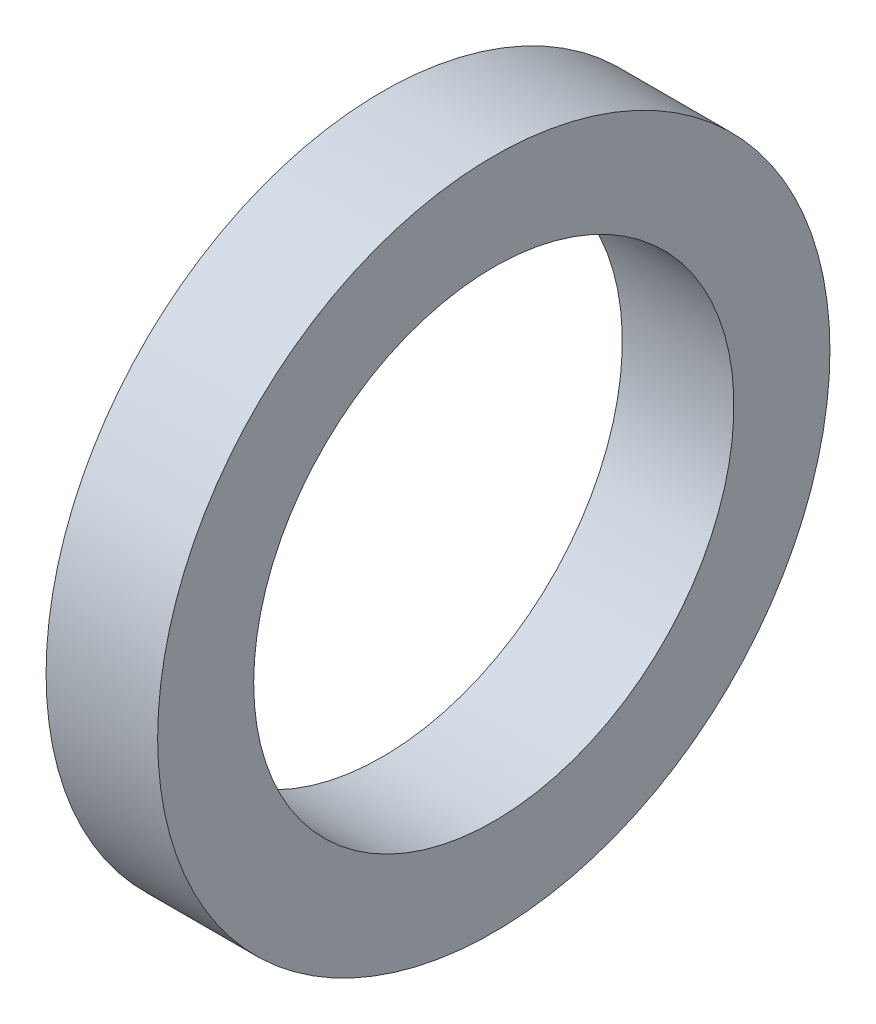
SolidWorks part; units mm, degrees
ref_plane "Front Plane" through (0, 0, 0) normal (0, 0, 1) x (1, 0, 0)
ref_plane "Top Plane" through (0, 0, 0) normal (0, 1, 0) x (1, 0, 0)
ref_plane "Right Plane" through (0, 0, 0) normal (1, 0, 0) x (0, 0, -1)
sketch "Sketch2" plane through (0, 0, 0) normal (0, 0, 1) x (1, 0, 0)
  line L0 (0, 0) -> (58.591, 0) construction
  line L2 (0, 0) -> (18.4, 0)
  line L3 (0, 0) -> (0, 2.5)
  line L4 (0, 2.5) -> (18.4, 2.5)
  line L5 (18.4, 0) -> (18.4, 2.5)
  line L6 (6.0094, 2.5) -> (6.0094, 6)
  line L11 (6.0094, 6) -> (9.9794, 6)
  line L16 (12.9794, 6) -> (12.9794, 3)
  line L17 (12.9794, 3) -> (13.6398, 3)
  line L18 (13.6398, 3) -> (13.6398, 2.5)
  line L19 (13.6398, 2.5) -> (6.0094, 2.5)
  line L22 (13.6398, 2.5) -> (16.1198, 2.5)
  line L23 (13.6398, 2.5) -> (13.6398, 4)
  line L24 (13.6398, 4) -> (16.1198, 4)
  line L25 (16.1198, 2.5) -> (16.1198, 4)
  line L27 (6.0094, 6) -> (9.9794, 6)
  line L28 (6.0094, 6) -> (6.0094, 9)
  line L29 (6.0094, 9) -> (9.9794, 9)
  line L30 (9.9794, 6) -> (9.9794, 9)
  line L31 (6.0094, 9) -> (6.0094, 8.25)
  line L32 (6.0094, 8.25) -> (5.0094, 8.25)
  line L33 (8.6609, 22.001) -> (8.6609, 12.476) construction
  line L34 (5.0094, 12.476) -> (12.3124, 12.476)
  line L35 (9.9794, 9) -> (12.3124, 9)
  line L36 (5.0094, 7.9375) -> (1.7709, 7.9375)
  line L37 (5.0094, 8.25) -> (5.0094, 12.476)
  line L38 (5.0094, 7.9375) -> (5.0094, 13.9365)
  line L39 (5.0094, 13.9365) -> (1.7709, 13.9365)
  line L40 (1.7709, 7.9375) -> (1.7709, 13.9365)
  line L41 (5.0094, 22.001) -> (12.3124, 22.001)
  line L42 (5.0094, 22.001) -> (5.0094, 30.1625)
  line L43 (5.0094, 30.1625) -> (12.3124, 30.1625)
  line L44 (12.3124, 22.001) -> (12.3124, 30.1625)
  line L49 (16.6398, 22.001) -> (16.6398, 7.5)
  line L51 (23.0198, 7.5) -> (23.0198, 6.5)
  line L54 (16.1198, 4) -> (13.6398, 4)
  line L56 (18.0398, 7.5) -> (23.0198, 7.5)
  line L57 (13.3124, 22.001) -> (16.6398, 22.001)
  line L58 (16.1198, 3.5) -> (20.0198, 3.5)
  line L59 (29.9098, 14) -> (26.9098, 11)
  line L60 (4.0094, 31.75) -> (18.0398, 31.75)
  line L61 (18.0398, 7.5) -> (23.0198, 7.5)
  line L62 (18.0398, 7.5) -> (18.0398, 12)
  line L63 (18.0398, 12) -> (23.0198, 12)
  line L64 (23.0198, 7.5) -> (23.0198, 12)
  line L65 (18.0398, 31.75) -> (18.0398, 12)
  line L66 (23.0198, 11) -> (26.9098, 11)
  line L67 (34.8098, 23) -> (31.3098, 19.5)
  line L68 (35.8098, 31) -> (38.7998, 33.99)
  line L69 (29.9098, 14) -> (29.9098, 15)
  line L70 (29.9098, 15) -> (22.9398, 15)
  line L71 (22.9398, 15) -> (21.0398, 15)
  line L72 (18.0398, 7.5) -> (16.6398, 7.5)
  line L73 (21.0398, 15) -> (21.0398, 43)
  line L74 (19.6115, 40) -> (9.6516, 40)
  line L75 (9.6516, 40) -> (4.0094, 40)
  line L76 (21.0398, 43) -> (19.6115, 43)
  line L77 (22.9398, 15) -> (29.9098, 15)
  line L78 (22.9398, 15) -> (22.9398, 21)
  line L79 (22.9398, 21) -> (29.9098, 21)
  line L80 (29.9098, 15) -> (29.9098, 21)
  line L81 (9.6516, 40) -> (19.6115, 40)
  line L82 (9.6516, 40) -> (9.6516, 50)
  line L83 (9.6516, 50) -> (19.6115, 50)
  line L84 (19.6115, 40) -> (19.6115, 50)
  line L85 (4.0094, 40) -> (4.0094, 31.75)
  line L86 (12.9794, 3) -> (12.9794, 2.5)
  line L87 (31.3098, 19.5) -> (29.9098, 19.5)
  line L88 (21.4694, 63.5) -> (21.4694, 51.308)
  line L89 (21.4694, 63.5) -> (25.9398, 63.5)
  line L90 (25.9398, 63.5) -> (25.9398, 25)
  line L91 (27.8398, 25) -> (25.9398, 25)
  line L92 (9.6516, 48) -> (8.2233, 48)
  line L93 (8.2233, 48) -> (8.2233, 53.476)
  line L94 (8.2233, 53.476) -> (19.6115, 53.476)
  line L95 (19.6115, 53.476) -> (19.6115, 50)
  line L96 (13.9174, 63.001) -> (13.9174, 53.476) construction
  line L97 (8.2233, 63.001) -> (19.6115, 63.001)
  line L98 (8.2233, 63.001) -> (8.2233, 68.2625)
  line L99 (8.2233, 68.2625) -> (19.6115, 68.2625)
  line L100 (19.6115, 63.001) -> (19.6115, 68.2625)
  line L101 (12.9794, 6) -> (11.9794, 6)
  line L102 (8.2233, 44.825) -> (4.9848, 44.825)
  line L103 (8.2233, 44.825) -> (8.2233, 54.9365)
  line L104 (8.2233, 54.9365) -> (4.9848, 54.9365)
  line L106 (9.9794, 6) -> (10.8794, 6)
  line L107 (27.8398, 25) -> (34.8098, 25)
  line L108 (34.8098, 25) -> (34.8098, 23)
  line L109 (0, 0) -> (-2, 0)
  line L110 (0, 0) -> (0, 11)
  line L111 (27.8398, 25) -> (34.8098, 25)
  line L112 (27.8398, 25) -> (27.8398, 32.5)
  line L113 (27.8398, 32.5) -> (34.8098, 32.5)
  line L114 (34.8098, 25) -> (34.8098, 32.5)
  line L115 (35.8098, 31) -> (34.8098, 31)
  line L116 (27.8398, 32.5) -> (27.8398, 64.5)
  line L117 (20.5849, 74.025) -> (6.2499, 74.025)
  line L118 (6.2499, 74.025) -> (6.2499, 76.2)
  line L119 (38.7998, 47.29) -> (30.8398, 55.25)
  line L120 (0, 11) -> (-2, 11)
  line L121 (38.7998, 43.815) -> (30.8623, 43.815)
  line L123 (-4.8152, 69.85) -> (1.5348, 76.2)
  line L124 (38.7998, 47.29) -> (38.7998, 33.99)
  line L125 (-2, 0) -> (-2, 11)
  line L126 (38.7998, 37.465) -> (30.8623, 37.465)
  line L127 (30.8623, 43.815) -> (30.8623, 37.465)
  line L128 (6.0094, 2.5) -> (6.0094, 0)
  line L129 (-0.0152, 63.5) -> (-0.0152, 30)
  line L132 (4.9848, 63.5) -> (-0.0152, 63.5)
  line L136 (-1.8152, 30) -> (-11.7752, 30)
  line L138 (-13.7752, 25.4) -> (-2, 25.4)
  line L139 (-2, 25.4) -> (-2, 11.5)
  line L140 (27.8398, 64.5) -> (20.5849, 64.5)
  line L141 (-1.8152, 30) -> (-11.7752, 30)
  line L142 (-1.8152, 30) -> (-1.8152, 39)
  line L143 (-1.8152, 39) -> (-11.7752, 39)
  line L144 (-11.7752, 30) -> (-11.7752, 39)
  line L145 (20.5849, 64.5) -> (20.5849, 74.025)
  line L146 (-12.7752, 37) -> (-12.7752, 47.29)
  line L147 (-12.7752, 37) -> (-11.7752, 37)
  line L148 (30.8398, 55.25) -> (30.8398, 76.2)
  line L149 (11.9794, 6) -> (11.9794, 5.45)
  line L154 (-2, 11.5) -> (0.5, 11.5)
  line L155 (4.9848, 60.6197) -> (24.0348, 60.6197)
  line L160 (4.9848, 60.6197) -> (4.9848, 55.8572)
  line L161 (4.9848, 55.8572) -> (24.0348, 55.8572)
  line L166 (24.0348, 60.6197) -> (24.0348, 55.8572)
  line L167 (4.9848, 60.6197) -> (24.0348, 55.8572) construction
  line L172 (4.9848, 55.8572) -> (24.0348, 60.6197) construction
  line L173 (24.0348, 62.2072) -> (25.9398, 62.2072)
  line L174 (11.9794, 5.45) -> (10.8794, 5.45)
  line L175 (10.8794, 6) -> (10.8794, 5.45)
  line L176 (24.0348, 62.2072) -> (24.0348, 54.2697)
  line L177 (24.0348, 54.2697) -> (25.9398, 54.2697)
  line L178 (25.9398, 62.2072) -> (25.9398, 54.2697)
  line L179 (24.0348, 62.2072) -> (25.9398, 54.2697) construction
  line L180 (24.0348, 54.2697) -> (25.9398, 62.2072) construction
  line L181 (3, 19.6197) -> (15.7, 19.6197)
  line L182 (3, 19.6197) -> (3, 14.8572)
  line L183 (3, 14.8572) -> (15.7, 14.8572)
  line L184 (15.7, 19.6197) -> (15.7, 14.8572)
  line L185 (3, 19.6197) -> (15.7, 14.8572) construction
  line L186 (3, 14.8572) -> (15.7, 19.6197) construction
  line L187 (15.7, 21.2072) -> (16.6398, 21.2072)
  line L188 (15.7, 21.2072) -> (15.7, 13.2697)
  line L189 (15.7, 13.2697) -> (16.6398, 13.2697)
  line L190 (16.6398, 21.2072) -> (16.6398, 13.2697)
  line L191 (15.7, 21.2072) -> (16.6398, 13.2697) construction
  line L192 (15.7, 13.2697) -> (16.6398, 21.2072) construction
  line L193 (0.5, 11.5) -> (0.5, 6.9375)
  line L194 (0.5, 6.9375) -> (1.7709, 6.9375)
  line L195 (23.0198, 6.5) -> (20.0198, 3.5)
  line L196 (4.9848, 63.5) -> (4.9848, 54.9365)
  line L197 (3, 43.825) -> (4.9848, 43.825)
  line L198 (1.7709, 6.9375) -> (1.7709, 7.9375)
  line L199 (6.0094, 0) -> (12.9794, 0)
  line L200 (12.9794, 0) -> (12.9794, 2.5)
  line L201 (18.0398, 31.75) -> (18.0398, 35.875)
  line L202 (18.0398, 35.875) -> (21.0398, 35.875)
  line L203 (30.8398, 76.2) -> (6.2499, 76.2)
  line L204 (2.8049, 69.85) -> (7.2499, 69.85) construction
  line L205 (7.2499, 67.4688) -> (26.2999, 67.4688)
  line L206 (7.2499, 74.025) -> (7.2499, 64.5)
  line L207 (7.2499, 64.5) -> (-1.8152, 64.5)
  line L208 (-1.8152, 64.5) -> (-1.8152, 39)
  line L209 (-12.7752, 47.29) -> (-4.8152, 55.25)
  line L210 (-4.8152, 55.25) -> (-4.8152, 69.85)
  line L211 (7.2499, 67.4688) -> (7.2499, 72.2312)
  line L212 (7.2499, 72.2312) -> (26.2999, 72.2313)
  line L213 (26.2999, 67.4688) -> (26.2999, 72.2313)
  line L214 (26.2999, 73.8187) -> (30.8398, 73.8187)
  line L215 (26.2999, 73.8187) -> (26.2999, 65.8813)
  line L216 (26.2999, 65.8813) -> (30.8398, 65.8813)
  line L217 (30.8398, 73.8187) -> (30.8398, 65.8813)
  line L218 (2.8049, 72.2313) -> (25.0299, 72.2313)
  line L219 (2.8049, 72.2313) -> (2.8049, 67.4687)
  line L220 (2.8049, 67.4687) -> (25.0299, 67.4687)
  line L221 (25.0299, 72.2313) -> (25.0299, 67.4687)
  line L222 (25.0299, 69.85) -> (20.5849, 69.85) construction
  line L223 (21.4694, 51.308) -> (22.9398, 51.308)
  line L224 (22.9398, 51.308) -> (22.9398, 21)
  line L225 (13.6398, 4) -> (13.6398, 12.2697)
  line L226 (13.6398, 12.2697) -> (13.3124, 12.2697)
  line L227 (13.3124, 12.2697) -> (13.3124, 22.001)
  line L228 (12.3124, 9) -> (12.3124, 12.476)
  line L229 (-1.8152, 30) -> (-0.0152, 30)
  line L230 (8.2233, 65.6317) -> (2.8049, 65.6317) construction
  line L231 (19.6115, 65.6317) -> (25.0299, 65.6317) construction
  line L232 (1.5348, 76.2) -> (6.2499, 76.2)
  line L233 (-11.7752, 30) -> (-13.7752, 30)
  line L234 (-13.7752, 30) -> (-13.7752, 25.4)
  line L235 (3, 13.9365) -> (3, 43.825)
  line L236 (4.9848, 54.9365) -> (4.9848, 44.825)
  line L237 (4.9848, 43.825) -> (4.9848, 44.825)
  circle A0 centre (26.8898, 25.95) radius 0.95
  circle A1 centre (21.9898, 15.95) radius 0.95
  circle A2 centre (17.3398, 8.2) radius 0.7
  circle A3 centre (10.4294, 6.45) radius 0.45
  circle A4 centre (-0.9152, 30.9) radius 0.9
  point P7 (24.9873, 58.2385)
  point P131 (16.1699, 17.2385)
  point P135 (14.5098, 58.2385)
  point P146 (9.35, 17.2385)
sketch "Sketch3" plane through (0, 0, 0) normal (0, 0, 1) x (1, 0, 0)
  line L0 (22.9398, 21) -> (29.9098, 21) construction
  line L1 (29.9098, 15) -> (29.9098, 21) construction
  line L2 (29.9098, 15) -> (22.9398, 15) construction
  line L3 (22.9398, 15) -> (22.9398, 21) construction
  line L4 (22.9398, 21) -> (29.9098, 21)
  line L5 (29.9098, 15) -> (29.9098, 21)
  line L6 (29.9098, 15) -> (22.9398, 15)
  line L7 (22.9398, 15) -> (22.9398, 21)
revolve "Revolve1" add sketch "Sketch3" angle 360 about L0
